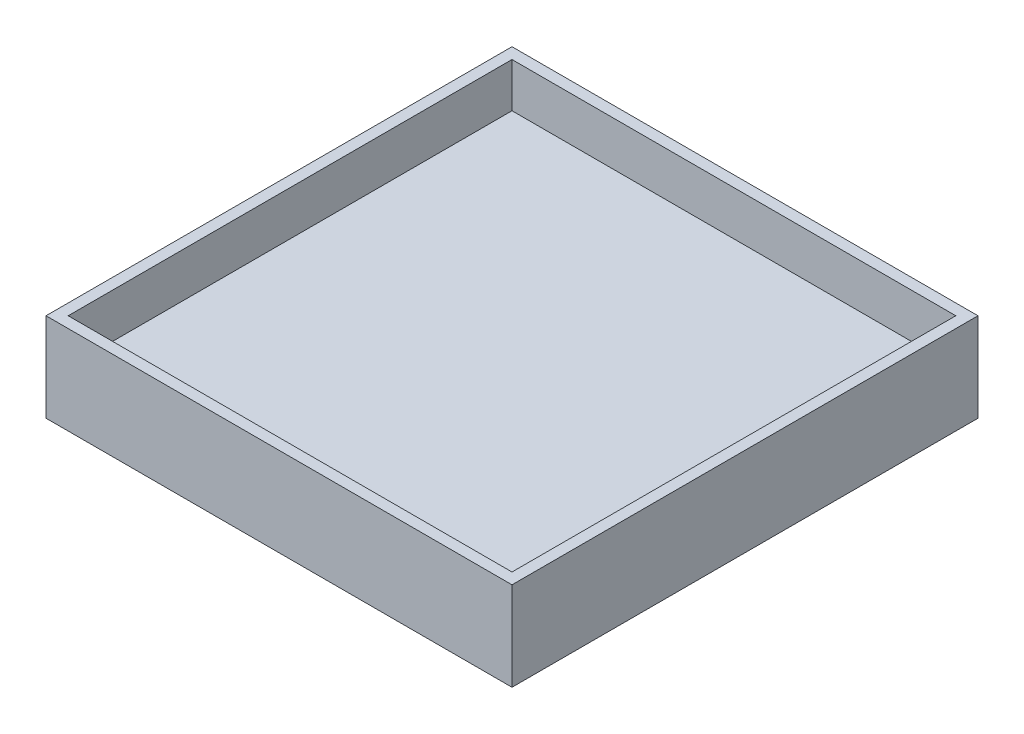
SolidWorks part; units mm, degrees
ref_plane "Front Plane" through (0, 0, 0) normal (0, 0, 1) x (1, 0, 0)
ref_plane "Top Plane" through (0, 0, 0) normal (0, 1, 0) x (1, 0, 0)
ref_plane "Right Plane" through (0, 0, 0) normal (1, 0, 0) x (0, 0, -1)
sketch "Sketch1" plane through (0, 0, 0) normal (0, 1, 0) x (1, 0, 0)
  line L1 (-500, -500) -> (500, -500)
  line L2 (-500, -500) -> (-500, 500)
  line L3 (-500, 500) -> (500, 500)
  line L4 (500, -500) -> (500, 500)
  line L5 (-500, -500) -> (500, 500) construction
  line L6 (-500, 500) -> (500, -500) construction
  point P0 (0, 0)
  dimension "D1" = 1000
  dimension "D2" = 1000
extrude "Boss-Extrude1" add sketch "Sketch1" along normal blind 100
sketch "Sketch2" plane through (0, 0, 0) normal (0, 1, 0) x (1, 0, 0)
  line L1 (-525, -525) -> (525, -525)
  line L2 (-525, -525) -> (-525, 525)
  line L3 (-525, 525) -> (525, 525)
  line L4 (525, -525) -> (525, 525)
  line L5 (-525, -525) -> (525, 525) construction
  line L6 (-525, 525) -> (525, -525) construction
  line L7 (-500, -500) -> (500, -500)
  line L8 (-500, -500) -> (-500, 500)
  line L9 (-500, 500) -> (500, 500)
  line L10 (500, -500) -> (500, 500)
  line L11 (-500, -500) -> (500, 500) construction
  line L12 (-500, 500) -> (500, -500) construction
  point P0 (0, 0)
  point P6 (0, 0)
  point P12 (0, 0)
  point P13 (0, 0)
  dimension "D1" = 25
  dimension "D2" = 25
extrude "Boss-Extrude3" add sketch "Sketch2" along normal blind 200 contours L7 L10 L9 L8 | L1 L4 L3 L2
sketch "Sketch3" plane through (0, 0, 0) normal (0, -1, 0) x (1, 0, 0)
  line L1 (-12.5, 15) -> (12.5, 15)
  line L2 (-12.5, 15) -> (-12.5, -15)
  line L3 (-12.5, -15) -> (12.5, -15)
  line L4 (12.5, 15) -> (12.5, -15)
  line L5 (-12.5, 15) -> (12.5, -15) construction
  line L6 (-12.5, -15) -> (12.5, 15) construction
  point P0 (0, 0)
  dimension "D1" = 30
  dimension "D2" = 25
extrude "Boss-Extrude4" add sketch "Sketch3" along normal blind 25
fillet "Fillet1" radius 2.5 4 edges at (0, 0, -15) (12.5, 0, 0) (0, 0, 15) (-12.5, 0, 0)
fillet "Fillet2" radius 10 2 edges at (12.5, -25, 0) (-12.5, -25, 0)
sketch "Sketch5" plane through (0, 0, 0) normal (0, 0, 1) x (1, 0, 0)
  line L0 (2.5, -25) -> (-2.5, -25) construction
  line L1 (-12.5, -15) -> (-12.5, -2.5) construction
  circle A0 centre (0, -17.5) radius 5
  dimension "D1" = 10
  dimension "7.5" = 7.5
  dimension "D2" = 12.5
extrude "Boss-Extrude5" add sketch "Sketch5" along normal blind 32.5 and the other way blind 32.5
